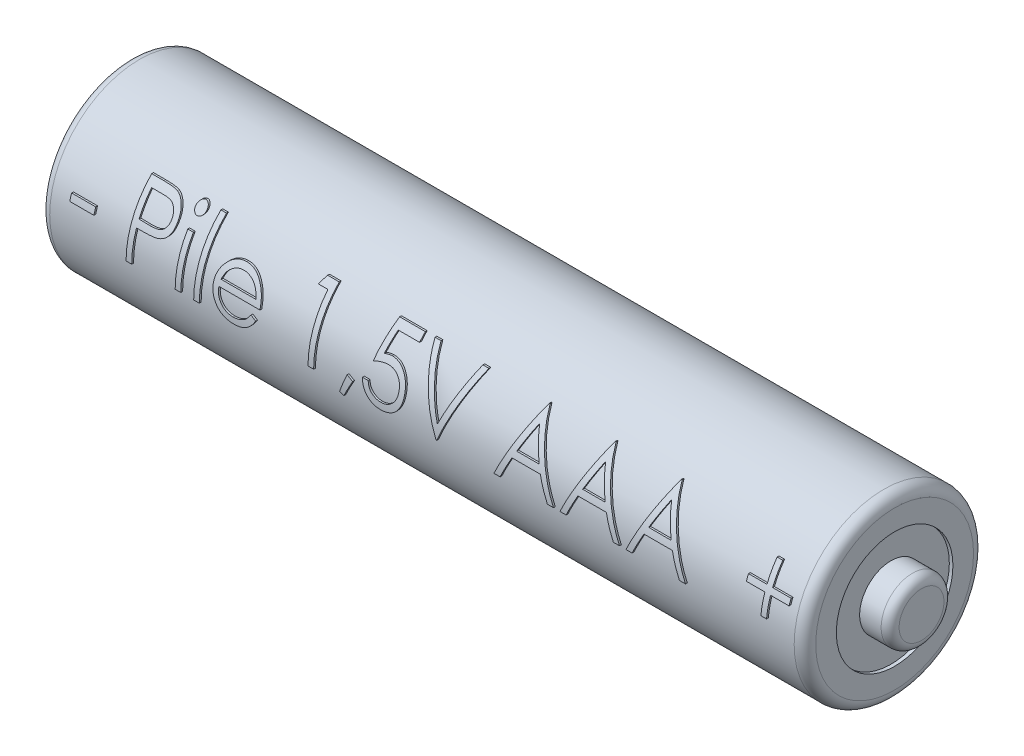
SolidWorks part; units mm, degrees
material "Acciaio al carbonio semplice"
ref_plane "Plan de face" through (0, 0, 0) normal (0, 0, 1) x (1, 0, 0)
ref_plane "Plan de dessus" through (0, 0, 0) normal (0, 1, 0) x (1, 0, 0)
ref_plane "Plan de droite" through (0, 0, 0) normal (1, 0, 0) x (0, 0, -1)
sketch "Esquisse1" plane through (0, 0, 0) normal (0, 0, 1) x (1, 0, 0)
  line L6 (0, 0) -> (0, 4)
  line L7 (0, 4) -> (-0.1, 4)
  line L8 (-0.1, 4) -> (-0.1, 4.5)
  line L9 (0.4, 5) -> (41.9, 5)
  line L10 (42.5, 4.4) -> (42.5, 3.25)
  line L11 (42.5, 3.25) -> (42.3, 3.25)
  line L12 (42.3, 3.25) -> (42.3, 1.75)
  line L13 (42.3, 1.75) -> (43.5, 1.75)
  line L14 (44, 1.25) -> (44, 0)
  line L15 (44, 0) -> (0, 0)
  arc A0 (0.4, 5) -> (-0.1, 4.5) centre (0.4, 4.5) ccw
  arc A1 (41.9, 5) -> (42.5, 4.4) centre (41.9, 4.4) cw
  arc A2 (43.5, 1.75) -> (44, 1.25) centre (43.5, 1.25) cw
  dimension "D8" = 0.5
  dimension "D11" = 0.6
  dimension "D14" = 0.5
  dimension "D5" = 1.75
  dimension "D6" = 5
  dimension "D7" = 42.5
  dimension "D9" = 0.1
  dimension "D10" = 4
  dimension "D12" = 3.25
  dimension "D13" = 0.2
  dimension "D15" = 44
revolve "Révolution1" add sketch "Esquisse1" angle 360 about L15
sketch "Esquisse2" plane through (0, 0, 0) normal (0, 0, 1) x (1, 0, 0)
  text T0 " - Pile 1,5V AAA  +"
extrude "Extrusion1" add sketch "Esquisse2" along normal offset from surface (4.962 mm away) 0.1
